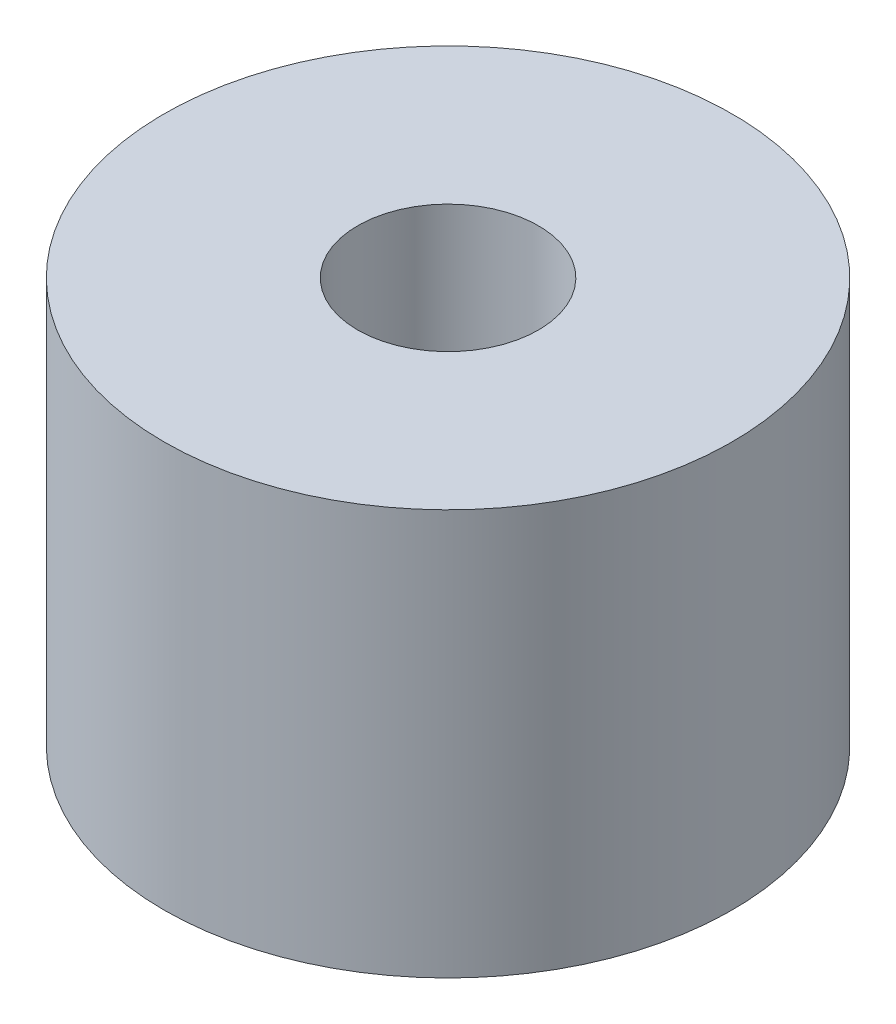
SolidWorks part; units mm, degrees
material "ABS"
ref_plane "Front Plane" through (0, 0, 0) normal (0, 0, 1) x (1, 0, 0)
ref_plane "Top Plane" through (0, 0, 0) normal (0, 1, 0) x (1, 0, 0)
ref_plane "Right Plane" through (0, 0, 0) normal (1, 0, 0) x (0, 0, -1)
sketch "Sketch1" plane through (0, 0, 0) normal (0, 1, 0) x (1, 0, 0)
  circle A0 centre (0, 0) radius 3.5
  circle A1 centre (0, 0) radius 11
  dimension "D1" = 7
  dimension "D2" = 22
extrude "Boss-Extrude1" add sketch "Sketch1" along normal blind 15.7
